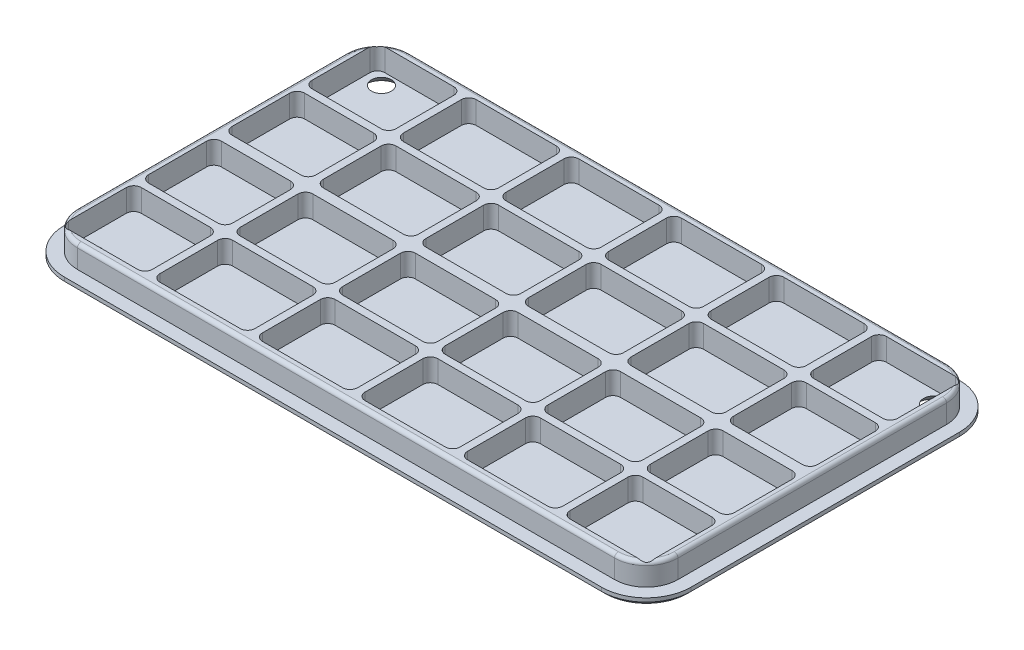
SolidWorks part; units mm, degrees
material "ABS"
ref_plane "Front Plane" through (0, 0, 0) normal (0, 0, 1) x (1, 0, 0)
ref_plane "Top Plane" through (0, 0, 0) normal (0, 1, 0) x (1, 0, 0)
ref_plane "Right Plane" through (0, 0, 0) normal (1, 0, 0) x (0, 0, -1)
sketch "Sketch1" plane through (0, 0, 0) normal (0, 1, 0) x (1, 0, 0)
  line L1 (-36, 24) -> (36, 24)
  line L2 (-42, 18) -> (-42, -18)
  line L3 (-36, -24) -> (36, -24)
  line L4 (42, 18) -> (42, -18)
  line L5 (-42, 24) -> (42, -24) construction
  line L6 (-42, -24) -> (42, 24) construction
  arc A0 (-36, 24) -> (-42, 18) centre (-36, 18) ccw
  arc A1 (42, 18) -> (36, 24) centre (36, 18) ccw
  arc A2 (42, -18) -> (36, -24) centre (36, -18) cw
  arc A3 (-42, -18) -> (-36, -24) centre (-36, -18) ccw
  point P0 (0, 0)
  dimension "D1" = 6
  dimension "D2" = 6
  dimension "D3" = 36
  dimension "D4" = 72
extrude "Boss-Extrude1" add sketch "Sketch1" along normal blind 1
chamfer "Chamfer1" distance 0.5 angle 45 8 edges at (-42, 0, 0) (-40.2426, 0, 22.2426) (0, 0, 24) (40.2426, 0, 22.2426) (42, 0, 0) (40.2426, 0, -22.2426) (0, 0, -24) (-40.2426, 0, -22.2426)
sketch "Sketch2" plane through (0, 1, 0) normal (0, 1, 0) x (1, 0, 0)
  line L1 (-36, 22.25) -> (36, 22.25)
  line L2 (-40.25, 18) -> (-40.25, -18)
  line L3 (-36, -22.25) -> (36, -22.25)
  line L4 (40.25, 18) -> (40.25, -18)
  line L5 (-40.25, 22.25) -> (40.25, -22.25) construction
  line L6 (-40.25, -22.25) -> (40.25, 22.25) construction
  arc A0 (-36, 22.25) -> (-40.25, 18) centre (-36, 18) ccw
  arc A1 (40.25, 18) -> (36, 22.25) centre (36, 18) ccw
  arc A2 (40.25, -18) -> (36, -22.25) centre (36, -18) cw
  arc A3 (-36, -22.25) -> (-40.25, -18) centre (-36, -18) cw
  point P0 (0, 0)
  dimension "D1" = 4.25
  dimension "D2" = 4.25
  dimension "D3" = 36
  dimension "D4" = 72
extrude "Boss-Extrude2" add sketch "Sketch2" along normal blind 3
hole_wizard "Hole2" positions "Sketch13" profile "Sketch14" legacy end condition up to next
sketch "Sketch13" plane through (0, 0, 0) normal (0, -1, 0) x (-1, 0, 0)
  line L0 (-41.5, 18) -> (-41.5, -18) construction
  line L1 (36, 23.5) -> (-36, 23.5) construction
  point P0 (-37, 19.5)
  dimension "D1" = 4.5
  dimension "D2" = 4
sketch "Sketch14" plane through (37, 0, -19.5) normal (1, 0, 0) x (0, 0, -1)
  line L0 (0, 0) -> (0, 4.7511)
  line L1 (0, 4.7511) -> (1.25, 4)
  line L2 (1.25, 4) -> (1.25, 1.0928)
  line L3 (1.25, 1.0928) -> (2.2, 0)
  line L4 (2.2, 0) -> (0, 0)
  line L5 (0, -14.3089) -> (0, 102.4216) construction
  line L6 (0, 4.7511) -> (-1.25, 4) construction
  line L7 (-1.25, 1.0928) -> (-2.2, 0) construction
  dimension "Diameter" = 2.5
  dimension "Depth" = 4
  dimension "C-Sink Diameter" = 4.4
  dimension "C-Sink Angle" = 82
  dimension "Drill Angle" = 118
fillet "Fillet2" radius 0.3 2 edges at (37, 0, -21.7) (37, 1.0928, -20.75)
mirror "Mirror9" about plane through (0, 0, 0) normal (1, 0, 0) of "Hole2"
mirror "Mirror10" about plane through (0, 0, 0) normal (0, 0, 1) of "Mirror9", "Hole2"
fillet "Fillet1" radius 0.5 8 edges at (-39.0052, 4, -21.0052) (0, 4, -22.25) (39.0052, 4, -21.0052) (40.25, 4, 0) (39.0052, 4, 21.0052) (0, 4, 22.25) (-39.0052, 4, 21.0052) (-40.25, 4, 0)
sketch "Sketch3" plane through (0, 4, 0) normal (0, 1, 0) x (1, 0, 0)
  line L0 (-40.25, -18) -> (-40.25, 18) construction
  line L1 (-38.25, 21.2) -> (-29, 21.2)
  line L2 (-39.25, 20.2) -> (-39.25, 12.45)
  line L3 (-38.25, 11.45) -> (-29, 11.45)
  line L4 (-28, 20.2) -> (-28, 12.45)
  line L5 (-39.25, 21.2) -> (-28, 11.45) construction
  line L6 (-39.25, 11.45) -> (-28, 21.2) construction
  line L7 (-36, 22.25) -> (36, 22.25) construction
  arc A0 (-28, 20.2) -> (-29, 21.2) centre (-29, 20.2) ccw
  arc A1 (-29, 11.45) -> (-28, 12.45) centre (-29, 12.45) ccw
  arc A2 (-38.25, 11.45) -> (-39.25, 12.45) centre (-38.25, 12.45) cw
  arc A3 (-38.25, 21.2) -> (-39.25, 20.2) centre (-38.25, 20.2) ccw
  point P0 (-33.625, 16.325)
  dimension "D3" = 1
  dimension "D1" = 11.25
  dimension "D2" = 9.75
  dimension "D4" = 1
  dimension "D5" = 1.05
extrude "Cut-Extrude1" cut sketch "Sketch3" against normal blind 3
sketch "Sketch5" plane through (0, 4, 0) normal (0, 1, 0) x (1, 0, 0)
  line L1 (-38.25, 10.45) -> (-29, 10.45)
  line L2 (-39.25, 9.45) -> (-39.25, 1.7)
  line L3 (-38.25, 0.7) -> (-29, 0.7)
  line L4 (-28, 9.45) -> (-28, 1.7)
  line L5 (-39.25, 10.45) -> (-28, 0.7) construction
  line L6 (-39.25, 0.7) -> (-28, 10.45) construction
  line L8 (-39.25, 19.8708) -> (-39.25, 12.45) construction
  line L9 (-38.25, 11.45) -> (-29, 11.45) construction
  arc A0 (-28, 9.45) -> (-29, 10.45) centre (-29, 9.45) ccw
  arc A1 (-29, 0.7) -> (-28, 1.7) centre (-29, 1.7) ccw
  arc A2 (-38.25, 0.7) -> (-39.25, 1.7) centre (-38.25, 1.7) cw
  arc A3 (-38.25, 10.45) -> (-39.25, 9.45) centre (-38.25, 9.45) ccw
  point P0 (-33.625, 5.575)
  dimension "D3" = 1
  dimension "D1" = 11.25
  dimension "D2" = 9.75
  dimension "D4" = 1
extrude "Cut-Extrude2" cut sketch "Sketch5" against normal blind 3
sketch "Sketch6" plane through (0, 4, 0) normal (0, 1, 0) x (1, 0, 0)
  line L1 (-26, 21.2) -> (-15.25, 21.2)
  line L2 (-27, 20.2) -> (-27, 12.45)
  line L3 (-26, 11.45) -> (-15.25, 11.45)
  line L4 (-14.25, 20.2) -> (-14.25, 12.45)
  line L5 (-27, 21.2) -> (-14.25, 11.45) construction
  line L6 (-27, 11.45) -> (-14.25, 21.2) construction
  line L8 (-28, 12.45) -> (-28, 20.2) construction
  line L9 (-38.25, 11.45) -> (-29, 11.45) construction
  arc A0 (-14.25, 20.2) -> (-15.25, 21.2) centre (-15.25, 20.2) ccw
  arc A1 (-15.25, 11.45) -> (-14.25, 12.45) centre (-15.25, 12.45) ccw
  arc A2 (-26, 11.45) -> (-27, 12.45) centre (-26, 12.45) cw
  arc A3 (-26, 21.2) -> (-27, 20.2) centre (-26, 20.2) ccw
  point P0 (-20.625, 16.325)
  dimension "D3" = 1
  dimension "D1" = 12.75
  dimension "D2" = 9.75
  dimension "D5" = 1
extrude "Cut-Extrude3" cut sketch "Sketch6" against normal blind 3
sketch "Sketch7" plane through (0, 4, 0) normal (0, 1, 0) x (1, 0, 0)
  line L1 (-26, 10.45) -> (-15.25, 10.45)
  line L2 (-27, 9.45) -> (-27, 1.7)
  line L3 (-26, 0.7) -> (-15.25, 0.7)
  line L4 (-14.25, 9.45) -> (-14.25, 1.7)
  line L5 (-27, 10.45) -> (-14.25, 0.7) construction
  line L6 (-27, 0.7) -> (-14.25, 10.45) construction
  line L10 (-27, 20.2) -> (-27, 12.45) construction
  line L11 (-29, 10.45) -> (-38.25, 10.45) construction
  arc A0 (-14.25, 9.45) -> (-15.25, 10.45) centre (-15.25, 9.45) ccw
  arc A1 (-15.25, 0.7) -> (-14.25, 1.7) centre (-15.25, 1.7) ccw
  arc A2 (-26, 0.7) -> (-27, 1.7) centre (-26, 1.7) cw
  arc A3 (-26, 10.45) -> (-27, 9.45) centre (-26, 9.45) ccw
  point P0 (-20.625, 5.575)
  dimension "D3" = 1
  dimension "D1" = 12.75
  dimension "D2" = 9.75
extrude "Cut-Extrude4" cut sketch "Sketch7" against normal blind 3
sketch "Sketch9" plane through (0, 4, 0) normal (0, 1, 0) x (1, 0, 0)
  line L0 (-26, 11.45) -> (-15.25, 11.45) construction
  line L1 (-12.25, 21.2) -> (-1.5, 21.2)
  line L2 (-13.25, 20.2) -> (-13.25, 12.45)
  line L3 (-12.25, 11.45) -> (-1.5, 11.45)
  line L4 (-0.5, 20.2) -> (-0.5, 12.45)
  line L5 (-13.25, 21.2) -> (-0.5, 11.45) construction
  line L6 (-13.25, 11.45) -> (-0.5, 21.2) construction
  line L7 (-14.25, 12.45) -> (-14.25, 20.2) construction
  arc A0 (-0.5, 20.2) -> (-1.5, 21.2) centre (-1.5, 20.2) ccw
  arc A1 (-1.5, 11.45) -> (-0.5, 12.45) centre (-1.5, 12.45) ccw
  arc A2 (-12.25, 11.45) -> (-13.25, 12.45) centre (-12.25, 12.45) cw
  arc A3 (-12.25, 21.2) -> (-13.25, 20.2) centre (-12.25, 20.2) ccw
  point P0 (-6.875, 16.325)
  dimension "D3" = 1
  dimension "D1" = 12.75
  dimension "D2" = 9.75
  dimension "D4" = 1
extrude "Cut-Extrude6" cut sketch "Sketch9" against normal blind 3
sketch "Sketch10" plane through (0, 4, 0) normal (0, 1, 0) x (1, 0, 0)
  line L1 (-12.25, 10.45) -> (-1.5, 10.45)
  line L2 (-13.25, 9.45) -> (-13.25, 1.7)
  line L3 (-12.25, 0.7) -> (-1.5, 0.7)
  line L4 (-0.5, 9.45) -> (-0.5, 1.7)
  line L5 (-13.25, 10.45) -> (-0.5, 0.7) construction
  line L6 (-13.25, 0.7) -> (-0.5, 10.45) construction
  line L9 (-15.25, 10.45) -> (-26, 10.45) construction
  line L10 (-13.25, 20.2) -> (-13.25, 12.45) construction
  arc A0 (-0.5, 9.45) -> (-1.5, 10.45) centre (-1.5, 9.45) ccw
  arc A1 (-1.5, 0.7) -> (-0.5, 1.7) centre (-1.5, 1.7) ccw
  arc A2 (-12.25, 0.7) -> (-13.25, 1.7) centre (-12.25, 1.7) cw
  arc A3 (-12.25, 10.45) -> (-13.25, 9.45) centre (-12.25, 9.45) ccw
  point P0 (-6.875, 5.575)
  dimension "D3" = 1
  dimension "D1" = 12.75
  dimension "D2" = 9.75
extrude "Cut-Extrude7" cut sketch "Sketch10" against normal blind 3
mirror "Mirror7" about plane through (0, 0, 0) normal (1, 0, 0) of "Cut-Extrude2", "Cut-Extrude3", "Cut-Extrude4", "Cut-Extrude6", "Cut-Extrude7", "Cut-Extrude1"
mirror "Mirror8" about plane through (0, 0, 0) normal (0, 0, 1) of "Mirror7", "Cut-Extrude1", "Cut-Extrude2", "Cut-Extrude3", "Cut-Extrude4", "Cut-Extrude6", "Cut-Extrude7"
